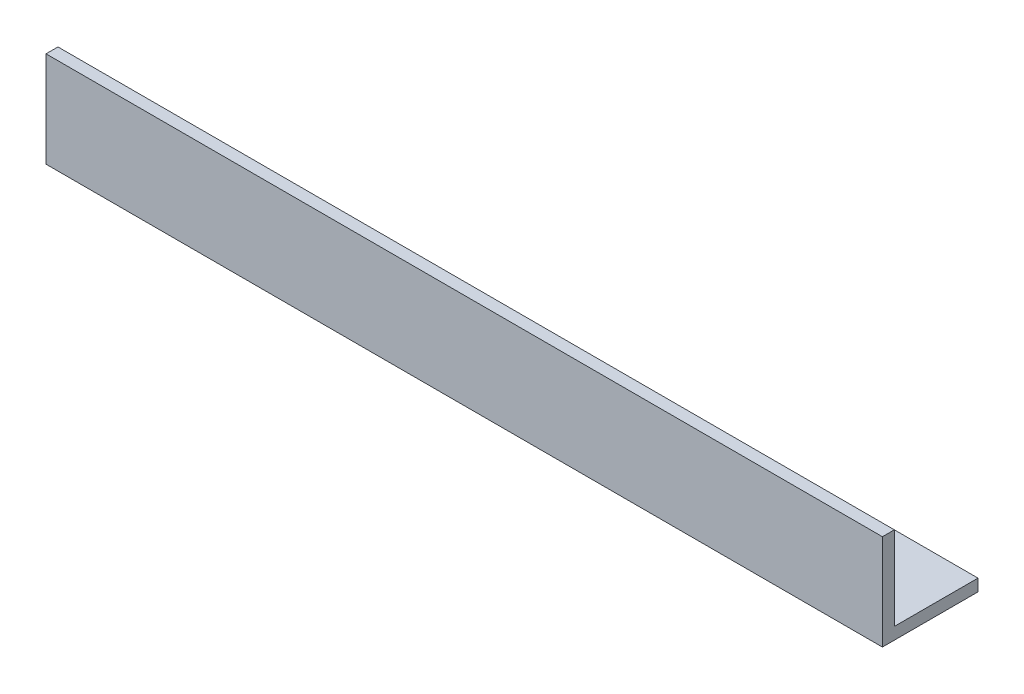
SolidWorks part; units mm, degrees
ref_plane "Front Plane" through (0, 0, 0) normal (0, 0, 1) x (1, 0, 0)
ref_plane "Top Plane" through (0, 0, 0) normal (0, 1, 0) x (1, 0, 0)
ref_plane "Right Plane" through (0, 0, 0) normal (1, 0, 0) x (0, 0, -1)
sketch "Sketch1" plane through (0, 0, 0) normal (1, 0, 0) x (0, 0, -1)
  line L0 (0, 0) -> (0, 25.4)
  line L1 (0, 55) -> (0, -55) construction
  line L2 (0, 25.4) -> (3.175, 25.4)
  line L3 (3.175, 25.4) -> (3.175, 3.175)
  line L4 (3.175, 3.175) -> (25.4, 3.175)
  line L5 (25.4, 3.175) -> (25.4, 0)
  line L6 (55, 0) -> (-55, 0) construction
  line L7 (25.4, 0) -> (0, 0)
  dimension "D1" = 25.4
  dimension "D2" = 3.175
extrude "Boss-Extrude1" add sketch "Sketch1" along normal mid plane 222.25
